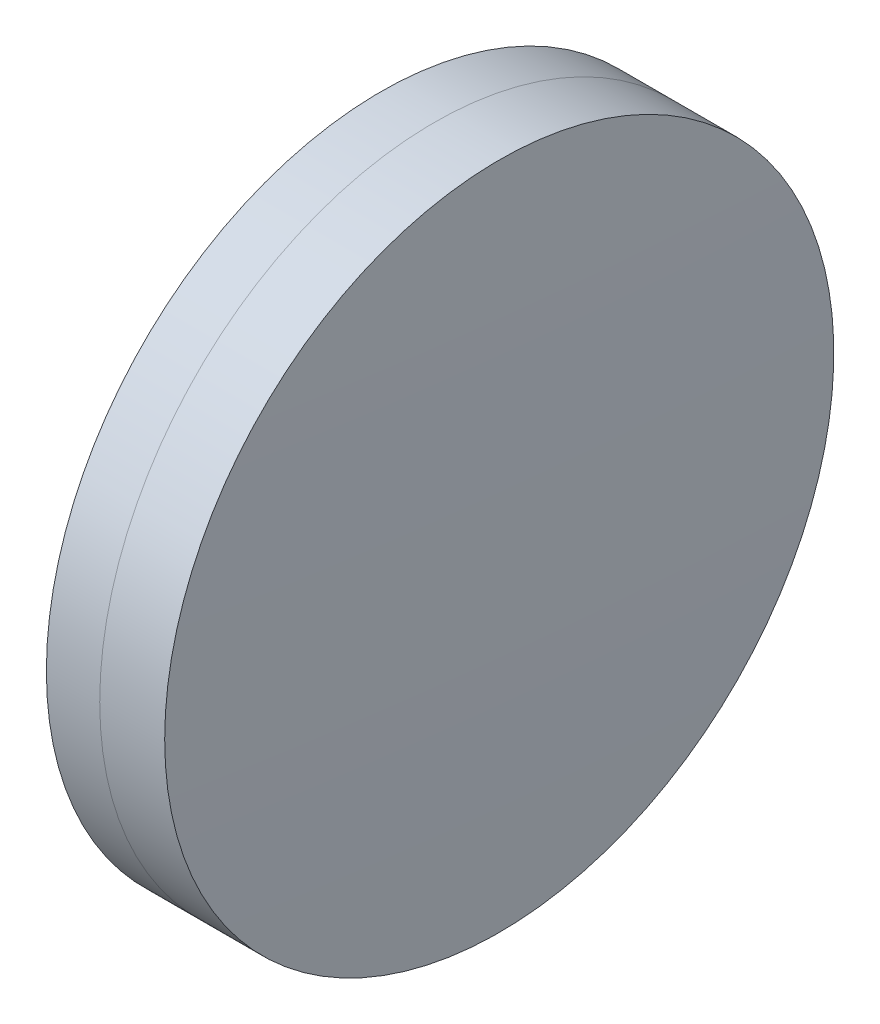
SolidWorks part; units mm, degrees
ref_plane "前视基准面" through (0, 0, 0) normal (0, 0, 1) x (1, 0, 0)
ref_plane "上视基准面" through (0, 0, 0) normal (0, 1, 0) x (1, 0, 0)
ref_plane "右视基准面" through (0, 0, 0) normal (1, 0, 0) x (0, 0, -1)
sketch "草图1" plane through (0, 0, 0) normal (0, 1, 0) x (1, 0, 0)
  line L0 (-9.7026, 0) -> (169.0175, 0) construction
  line L1 (140.0535, -12.5) -> (142.0468, -12.5)
  line L2 (140.0535, 12.5) -> (142.0468, 12.5)
  arc A0 (142.0468, -12.5) -> (142.0468, 12.5) centre (14.8797, 0) ccw
  arc A1 (140.0535, 12.5) -> (140.0535, -12.5) centre (333.3197, 0) ccw
  point P4 (169.0175, 0)
  point P10 (139.6497, 0)
  point P11 (142.6597, 0)
  dimension "D3" = 193.67
  dimension "D4" = 127.78
  dimension "D1" = 12.5
  dimension "D2" = 12.5
  dimension "D5" = 3.01
revolve "旋转1" add sketch "草图1" angle 360 about L0
sketch "草图2" plane through (0, 0, 0) normal (0, 1, 0) x (1, 0, 0)
  line L0 (-0.5519, 0) -> (159.0776, 0) construction
  line L2 (142.0468, 12.5) -> (144.4739, 12.5)
  line L3 (142.0468, -12.5) -> (144.4739, -12.5)
  arc A0 (144.4739, -12.5) -> (144.4739, 12.5) centre (-275.8903, 0) ccw
  arc A1 (142.0468, -12.5) -> (142.0468, 12.5) centre (14.8797, 0) ccw construction
  arc A2 (142.0468, -12.5) -> (142.0468, 12.5) centre (14.8797, 0) ccw
  point P4 (142.6597, 0)
  point P8 (144.6597, 0)
  point P9 (159.0776, 0)
  dimension "D1" = 420.55
  dimension "D2" = 2
revolve "旋转3" add sketch "草图2" angle 360 about L0
